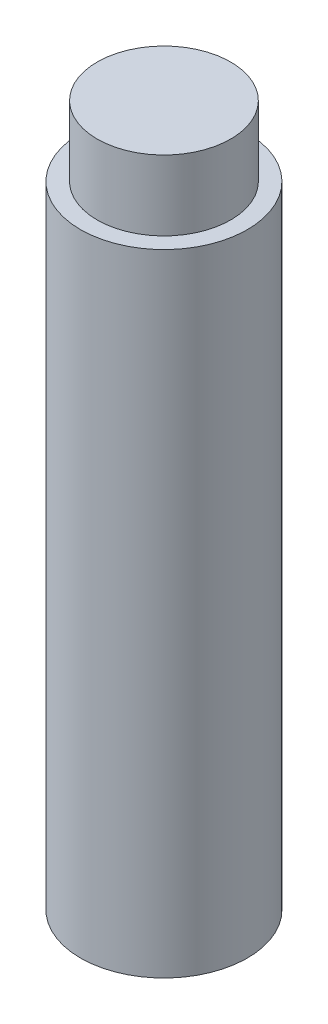
SolidWorks part; units mm, degrees
ref_plane "Front Plane" through (0, 0, 0) normal (0, 0, 1) x (1, 0, 0)
ref_plane "Top Plane" through (0, 0, 0) normal (0, 1, 0) x (1, 0, 0)
ref_plane "Right Plane" through (0, 0, 0) normal (1, 0, 0) x (0, 0, -1)
sketch "Sketch1" plane through (0, 0, 0) normal (0, 1, 0) x (1, 0, 0)
  circle A0 centre (0, 0) radius 2.3812
extrude "Boss-Extrude1" add sketch "Sketch1" along normal blind 20
sketch "Sketch2" plane through (0, 20, 0) normal (0, 1, 0) x (1, 0, 0)
  circle A0 centre (0, 0) radius 1.905
  circle A1 centre (0, 0) radius 2.3812
extrude "Cut-Extrude1" cut sketch "Sketch2" against normal blind 2
